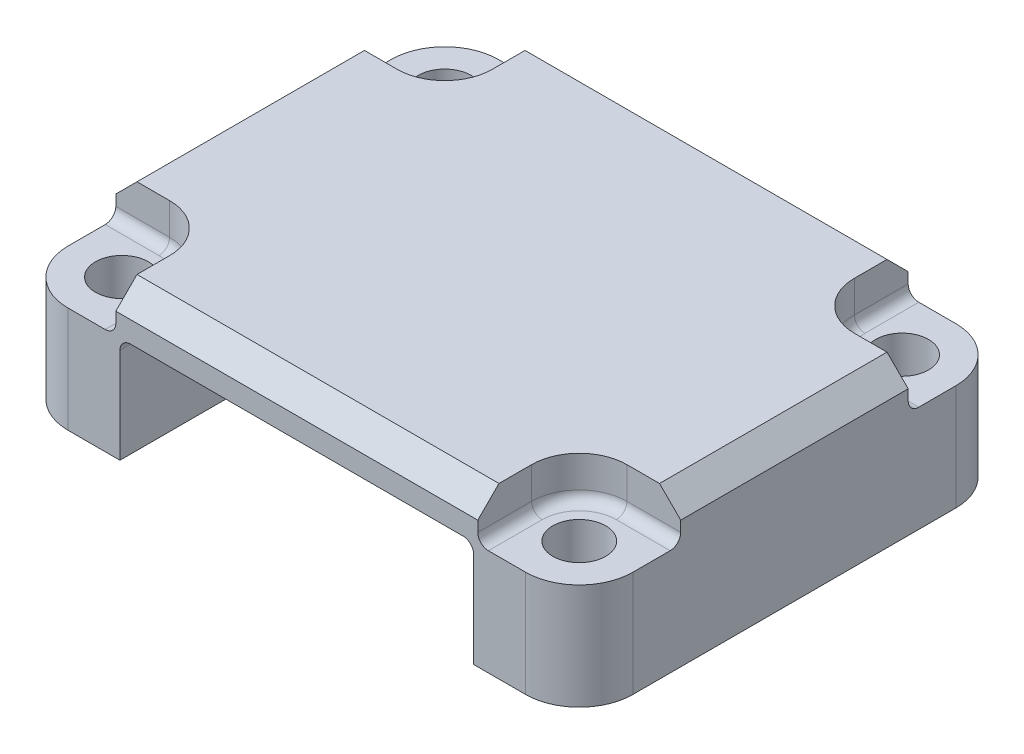
SolidWorks part; units mm, degrees
ref_plane "Front Plane" through (0, 0, 0) normal (0, 0, 1) x (1, 0, 0)
ref_plane "Top Plane" through (0, 0, 0) normal (0, 1, 0) x (1, 0, 0)
ref_plane "Right Plane" through (0, 0, 0) normal (1, 0, 0) x (0, 0, -1)
sketch "Sketch1" plane through (0, -16.1695, 0) normal (0, 1, 0) x (1, 0, 0)
  line L0 (-127.057, -71.4637) -> (-127.057, -86.7037) construction
  line L1 (-129.597, -89.2437) -> (-151.187, -89.2437) construction
  line L2 (-153.727, -86.7037) -> (-153.727, -71.4637) construction
  line L3 (-151.187, -68.9237) -> (-129.597, -68.9237) construction
  line L4 (-127.057, -71.4637) -> (-127.057, -86.7037)
  line L5 (-129.597, -89.2437) -> (-151.187, -89.2437)
  line L6 (-153.727, -86.7037) -> (-153.727, -71.4637)
  line L7 (-151.187, -68.9237) -> (-129.597, -68.9237)
  circle A1 centre (-151.187, -71.4637) radius 1.25
  circle A2 centre (-151.187, -86.7037) radius 1.25
  circle A3 centre (-129.597, -86.7037) radius 1.25
  circle A4 centre (-129.597, -71.4637) radius 1.25
  circle A6 centre (-151.187, -71.4637) radius 1.25 construction
  circle A7 centre (-129.597, -71.4637) radius 1.25 construction
  circle A8 centre (-129.597, -86.7037) radius 1.25 construction
  circle A9 centre (-151.187, -86.7037) radius 1.25 construction
  arc A10 (-127.057, -71.4637) -> (-129.597, -68.9237) centre (-129.597, -71.4637) ccw construction
  arc A11 (-129.597, -89.2437) -> (-127.057, -86.7037) centre (-129.597, -86.7037) ccw construction
  arc A12 (-153.727, -86.7037) -> (-151.187, -89.2437) centre (-151.187, -86.7037) ccw construction
  arc A13 (-151.187, -68.9237) -> (-153.727, -71.4637) centre (-151.187, -71.4637) ccw construction
  arc A14 (-127.057, -71.4637) -> (-129.597, -68.9237) centre (-129.597, -71.4637) ccw
  arc A15 (-129.597, -89.2437) -> (-127.057, -86.7037) centre (-129.597, -86.7037) ccw
  arc A16 (-153.727, -86.7037) -> (-151.187, -89.2437) centre (-151.187, -86.7037) ccw
  arc A17 (-151.187, -68.9237) -> (-153.727, -71.4637) centre (-151.187, -71.4637) ccw
extrude "Boss-Extrude1" add sketch "Sketch1" along normal blind 7
sketch "Sketch2" plane through (0, -16.1695, 0) normal (0, -1, 0) x (1, 0, 0)
  line L0 (-148.742, 89.2437) -> (-148.742, 68.9237)
  line L1 (-151.187, 89.2437) -> (-129.597, 89.2437) construction
  line L2 (-129.597, 68.9237) -> (-151.187, 68.9237) construction
  line L3 (-132.042, 89.2437) -> (-132.042, 68.9237)
  line L4 (-140.392, 89.2437) -> (-140.392, 68.9237) construction
  line L5 (-153.727, 71.4637) -> (-153.727, 86.7037) construction
  line L6 (-127.057, 86.7037) -> (-127.057, 71.4637) construction
  circle A2 centre (-146.742, 87.9737) radius 1 construction
  circle A3 centre (-146.742, 87.9737) radius 1 construction
  point P14 (-147.742, 87.9737)
  line M8 (-129.597, 89.2437) -> (-151.187, 89.2437)
  line M12 (-151.187, 68.9237) -> (-129.597, 68.9237)
  dimension "D1" = 1
extrude "Cut-Extrude1" cut sketch "Sketch2" against normal blind 5 contours L3 L0 M8 M12
sketch "Sketch3" plane through (0, -9.1695, 0) normal (0, 1, 0) x (1, 0, 0)
  line L0 (-131.847, -89.2437) -> (-131.847, -86.7037)
  line L1 (-151.187, -89.2437) -> (-129.597, -89.2437) construction
  line L2 (-129.597, -84.4537) -> (-127.057, -84.4537)
  line L3 (-127.057, -86.7037) -> (-127.057, -71.4637) construction
  line L4 (-159.9891, -79.0837) -> (-108.5393, -79.0837) construction
  line L5 (-140.392, -207.7535) -> (-140.392, -166.1623) construction
  line L7 (-129.597, -68.9237) -> (-151.187, -68.9237) construction
  line L8 (-153.727, -71.4637) -> (-153.727, -86.7037) construction
  line L9 (-151.187, -84.4537) -> (-153.727, -84.4537)
  line L10 (-148.937, -89.2437) -> (-148.937, -86.7037)
  line L11 (-129.597, -73.7137) -> (-127.057, -73.7137)
  line L12 (-131.847, -68.9237) -> (-131.847, -71.4637)
  line L13 (-151.187, -73.7137) -> (-153.727, -73.7137)
  line L14 (-148.937, -68.9237) -> (-148.937, -71.4637)
  arc A0 (-131.847, -86.7037) -> (-129.597, -84.4537) centre (-129.597, -86.7037) cw
  circle A1 centre (-129.597, -86.7037) radius 2.25 construction
  arc A2 (-148.937, -86.7037) -> (-151.187, -84.4537) centre (-151.187, -86.7037) ccw
  arc A3 (-131.847, -71.4637) -> (-129.597, -73.7137) centre (-129.597, -71.4637) ccw
  arc A4 (-148.937, -71.4637) -> (-151.187, -73.7137) centre (-151.187, -71.4637) cw
  point P25 (-131.188, -85.1127)
  point P28 (-131.188, -73.0547)
  circle M8 centre (-129.597, -86.7037) radius 1.25
  circle M9 centre (-151.187, -71.4637) radius 1.25
  arc M10 (-127.057, -71.4637) -> (-129.597, -68.9237) centre (-129.597, -71.4637) ccw
  line M11 (-129.597, -68.9237) -> (-151.187, -68.9237)
  arc M12 (-151.187, -68.9237) -> (-153.727, -71.4637) centre (-151.187, -71.4637) ccw
  line M13 (-153.727, -71.4637) -> (-153.727, -86.7037)
  arc M14 (-153.727, -86.7037) -> (-151.187, -89.2437) centre (-151.187, -86.7037) ccw
  line M15 (-151.187, -89.2437) -> (-129.597, -89.2437)
  arc M16 (-129.597, -89.2437) -> (-127.057, -86.7037) centre (-129.597, -86.7037) ccw
  line M17 (-127.057, -86.7037) -> (-127.057, -71.4637)
  circle M18 centre (-151.187, -86.7037) radius 1.25
  circle M19 centre (-129.597, -71.4637) radius 1.25
  dimension "D1" = 4.5
extrude "Cut-Extrude2" cut sketch "Sketch3" against normal blind 2 contours A0 L0 L2 M15 M16 M17 M8 | L10 A2 L9 M13 M14 M15 M18 | A4 L14 L13 M11 M12 M13 M9 | L12 A3 L11 M17 M10 M11 M19
chamfer "Chamfer1" distance 1 angle 45 4 edges at (-153.727, -9.1695, 79.0837) (-140.392, -9.1695, 68.9237) (-127.057, -9.1695, 79.0837) (-140.392, -9.1695, 89.2437)
fillet "Fillet1" radius 0.5 2 edges at (-132.042, -11.1695, 79.0837) (-148.742, -11.1695, 79.0837)
fillet "Fillet2" radius 0.5 12 edges at (-131.847, -11.1695, 70.1937) (-128.327, -11.1695, 73.7137) (-148.937, -11.1695, 70.1937) (-152.457, -11.1695, 73.7137) (-148.937, -11.1695, 87.9737) (-152.457, -11.1695, 84.4537) (-131.847, -11.1695, 87.9737) (-128.327, -11.1695, 84.4537) (-131.188, -11.1695, 73.0547) (-149.596, -11.1695, 73.0547) (-149.596, -11.1695, 85.1127) (-131.188, -11.1695, 85.1127)
